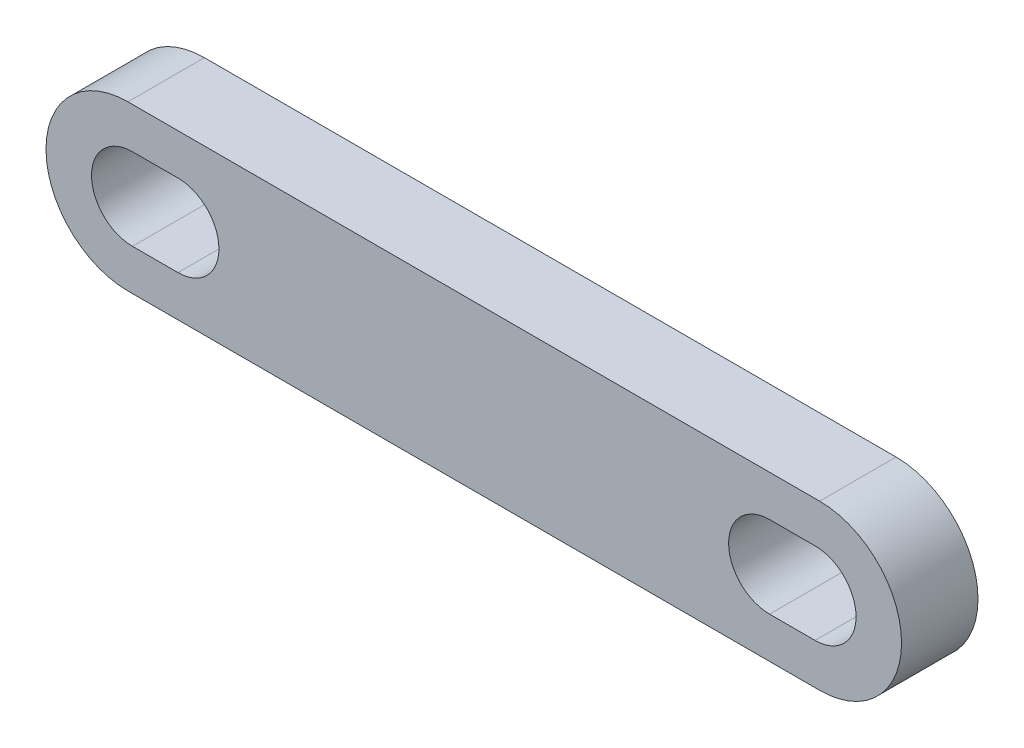
SolidWorks part; units mm, degrees
material "acero"
ref_plane "Alzado" through (0, 0, 0) normal (0, 0, 1) x (1, 0, 0)
ref_plane "Planta" through (0, 0, 0) normal (0, 1, 0) x (1, 0, 0)
ref_plane "Vista lateral" through (0, 0, 0) normal (1, 0, 0) x (0, 0, -1)
sketch "Croquis1" plane through (0, 0, 0) normal (0, 0, 1) x (1, 0, 0)
  line L2 (19, 4.5) -> (-19, 4.5)
  line L3 (-19, -4.5) -> (19, -4.5)
  line L4 (19, 4.5) -> (-19, 4.5)
  line L5 (-19, -4.5) -> (19, -4.5)
  line L10 (18.75, 2.25) -> (16.25, 2.25)
  line L11 (16.25, -2.25) -> (18.75, -2.25)
  line L12 (18.75, 2.25) -> (16.25, 2.25)
  line L13 (16.25, -2.25) -> (18.75, -2.25)
  line L14 (-16.25, 2.25) -> (-18.75, 2.25)
  line L15 (-18.75, -2.25) -> (-16.25, -2.25)
  line L16 (-16.25, 2.25) -> (-18.75, 2.25)
  line L17 (-18.75, -2.25) -> (-16.25, -2.25)
  arc A2 (-19, 4.5) -> (-19, -4.5) centre (-19, 0) ccw
  arc A3 (19, -4.5) -> (19, 4.5) centre (19, 0) ccw
  arc A4 (-19, 4.5) -> (-19, -4.5) centre (-19, 0) ccw
  arc A5 (19, -4.5) -> (19, 4.5) centre (19, 0) ccw
  arc A10 (16.25, 2.25) -> (16.25, -2.25) centre (16.25, 0) ccw
  arc A11 (18.75, -2.25) -> (18.75, 2.25) centre (18.75, 0) ccw
  arc A12 (16.25, 2.25) -> (16.25, -2.25) centre (16.25, 0) ccw
  arc A13 (18.75, -2.25) -> (18.75, 2.25) centre (18.75, 0) ccw
  arc A14 (-18.75, 2.25) -> (-18.75, -2.25) centre (-18.75, 0) ccw
  arc A15 (-16.25, -2.25) -> (-16.25, 2.25) centre (-16.25, 0) ccw
  arc A16 (-18.75, 2.25) -> (-18.75, -2.25) centre (-18.75, 0) ccw
  arc A17 (-16.25, -2.25) -> (-16.25, 2.25) centre (-16.25, 0) ccw
  dimension "D1" = 0
  dimension "D2" = 0
  dimension "D3" = 0
extrude "Saliente-Extruir2" add sketch "Croquis1" along normal blind 4.2
